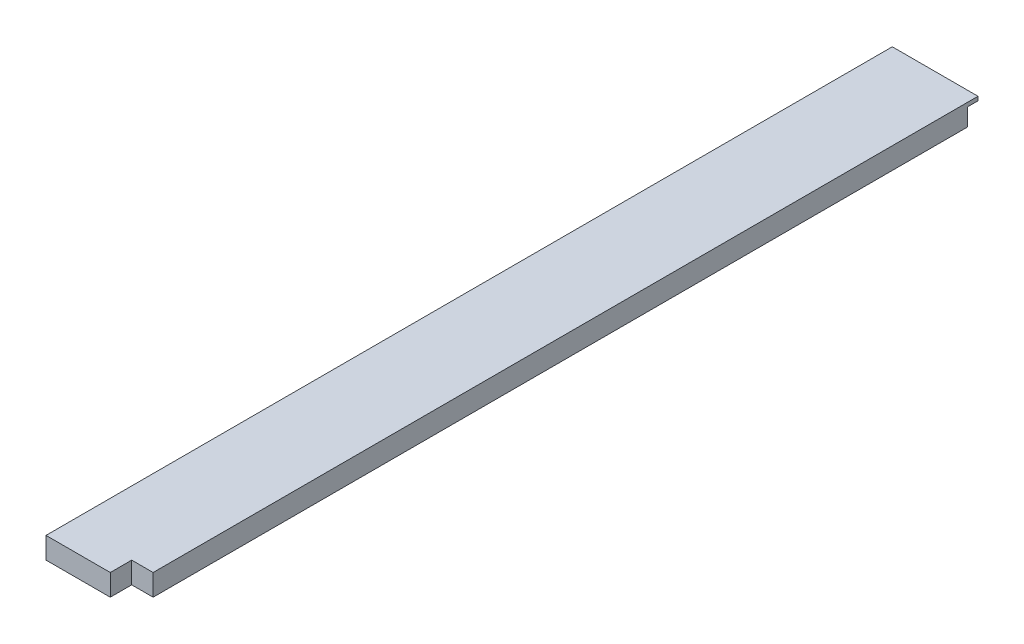
SolidWorks part; units mm, degrees
ref_plane "Front Plane" through (0, 0, 0) normal (0, 0, 1) x (1, 0, 0)
ref_plane "Top Plane" through (0, 0, 0) normal (0, 1, 0) x (1, 0, 0)
ref_plane "Right Plane" through (0, 0, 0) normal (1, 0, 0) x (0, 0, -1)
sketch "Sketch1" plane through (0, 0, 0) normal (0, 0, 1) x (1, 0, 0)
  line L0 (0, 12.7) -> (38.1, 12.7)
  line L3 (50.8, 6.35) -> (50.8, 0)
  line L4 (50.8, 0) -> (0, 0)
  line L5 (0, 0) -> (0, 12.7)
  line L6 (50.8, 6.35) -> (50.8, 12.7)
  line L7 (50.8, 12.7) -> (38.1, 12.7)
  dimension "D2" = 6.35
  dimension "D3" = 50.8
extrude "Boss-Extrude1" add sketch "Sketch1" along normal blind 501.65
sketch "Sketch3" plane through (0, 0, 0) normal (0, 1, 0) x (1, 0, 0)
  line L5 (0, -501.65) -> (0, 0) construction
  line L6 (0, -6.35) -> (50.8, -6.35)
  line L7 (0, -6.35) -> (0, 0)
  line L8 (0, 0) -> (50.8, 0)
  line L9 (50.8, -6.35) -> (50.8, 0)
  dimension "D1" = 6.35
extrude "Cut-Extrude1" cut sketch "Sketch3" along normal blind 10.3378
sketch "Sketch4" plane through (0, 0, 0) normal (0, -1, 0) x (1, 0, 0)
  line L1 (50.8, 501.65) -> (38.1, 501.65)
  line L2 (50.8, 501.65) -> (50.8, 488.95)
  line L3 (50.8, 488.95) -> (38.1, 488.95)
  line L4 (38.1, 501.65) -> (38.1, 488.95)
  dimension "D1" = 12.7
  dimension "D2" = 12.7
extrude "Cut-Extrude4" cut sketch "Sketch4" against normal through all
